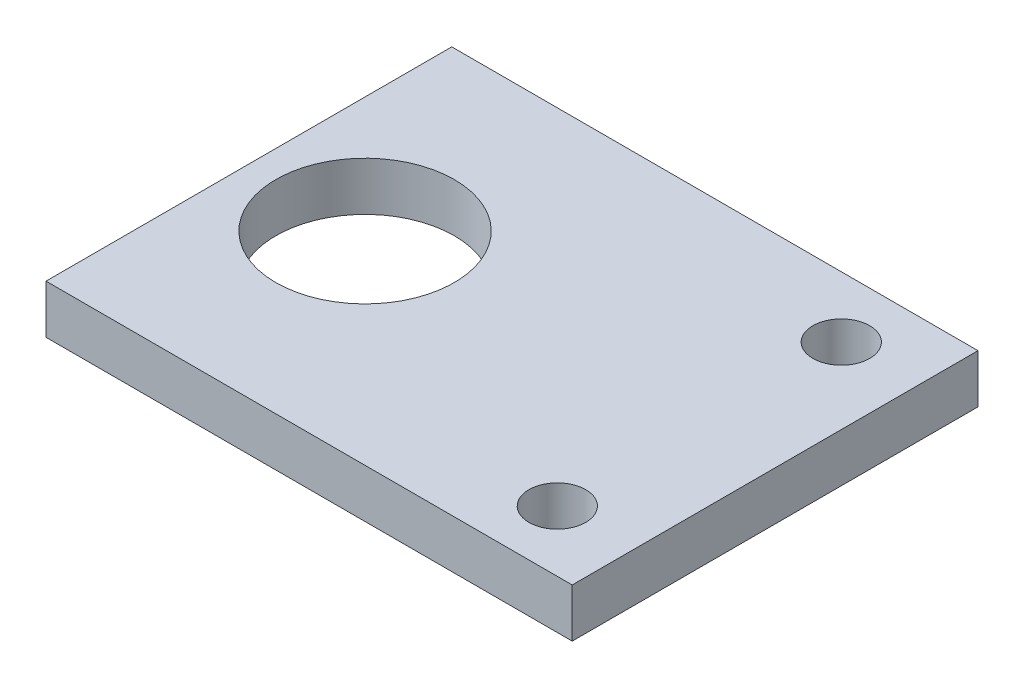
SolidWorks part; units mm, degrees
ref_plane "Front Plane" through (0, 0, 0) normal (0, 0, 1) x (1, 0, 0)
ref_plane "Top Plane" through (0, 0, 0) normal (0, 1, 0) x (1, 0, 0)
ref_plane "Right Plane" through (0, 0, 0) normal (1, 0, 0) x (0, 0, -1)
sketch "Sketch1" plane through (0, 0, 0) normal (0, 1, 0) x (1, 0, 0)
  line L0 (0, 61.7725) -> (0, -64.7928) construction
  line L3 (-26.0804, -8) -> (-26.0804, 8)
  line L6 (-9.001, 12.5039) -> (6.3491, 12.5039)
  line L7 (6.3491, 12.5039) -> (6.3491, 8)
  line L8 (-4.6226, 0) -> (9.2617, 0) construction
  line L9 (6.3491, -12.5039) -> (6.3491, -8)
  line L10 (-9.001, -12.5039) -> (6.3491, -12.5039)
  line L12 (6.3491, 8) -> (6.3491, -8)
  line L13 (-26.0804, 8) -> (-26.0804, 12.5039)
  line L14 (-26.0804, 12.5039) -> (-9.001, 12.5039)
  line L15 (-26.0804, -12.5039) -> (-9.001, -12.5039)
  line L16 (-26.0804, -8) -> (-26.0804, -12.5039)
  circle A0 centre (-18.922, 0) radius 9.5
  circle A1 centre (1.678, 8.75) radius 1.75
  circle A2 centre (1.678, -8.75) radius 1.75
  circle A3 centre (-18.922, 0) radius 5.5
  point P3 (0, 0)
  dimension "D1" = 11
  dimension "D2" = 20.6
  dimension "D3" = 19
  dimension "D4" = 8.75
extrude "Boss-Extrude1" add sketch "Sketch1" along normal blind 3 contours L3 L16 L15 L10 L9 L12 L7 L6 L14 L13 A0 A1 A2 | A0 A3
